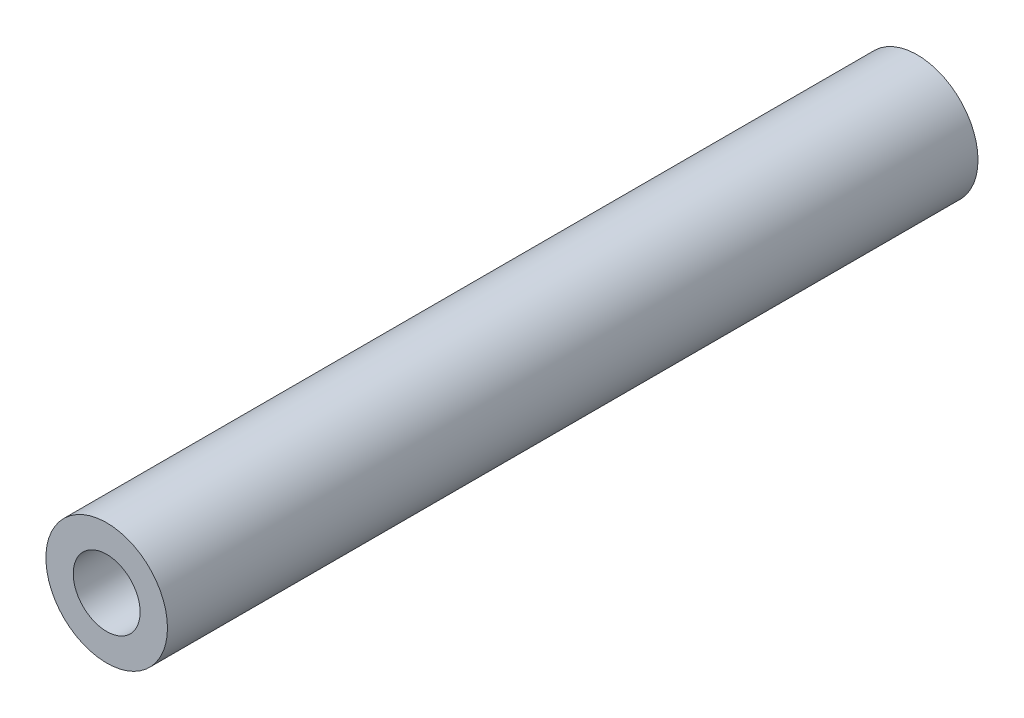
SolidWorks part; units mm, degrees
material "6061 合金"
ref_plane "前视基准面" through (0, 0, 0) normal (0, 0, 1) x (1, 0, 0)
ref_plane "上视基准面" through (0, 0, 0) normal (0, 1, 0) x (1, 0, 0)
ref_plane "右视基准面" through (0, 0, 0) normal (1, 0, 0) x (0, 0, -1)
sketch "草图1" plane through (0, 0, 0) normal (0, 0, 1) x (1, 0, 0)
  circle A0 centre (0, 0) radius 1.65
  circle A1 centre (0, 0) radius 3
  dimension "D1" = 3.3
  dimension "D2" = 6
extrude "凸台-拉伸1" add sketch "草图1" along normal blind 40
